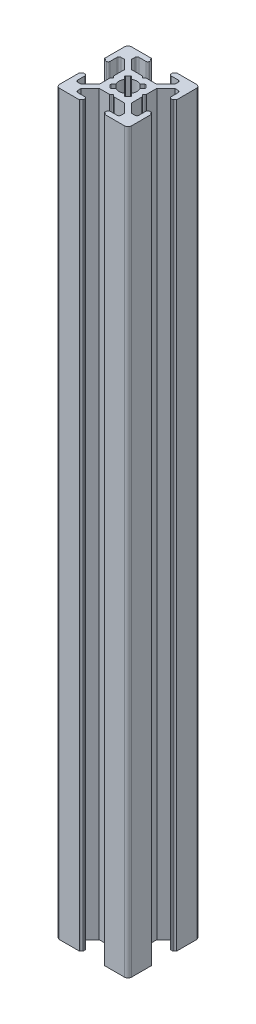
SolidWorks part; units mm, degrees
ref_plane "Front Plane" through (0, 0, 0) normal (0, 0, 1) x (1, 0, 0)
ref_plane "Top Plane" through (0, 0, 0) normal (0, 1, 0) x (1, 0, 0)
ref_plane "Right Plane" through (0, 0, 0) normal (1, 0, 0) x (0, 0, -1)
sketch "Sketch3" plane through (0, 0, 0) normal (0, 1, 0) x (1, 0, 0)
  line L0 (7, 20) -> (7, 18.5)
  line L1 (0, 0) -> (20, 0)
  line L2 (0, 0) -> (0, 20)
  line L3 (0, 20) -> (20, 20)
  line L4 (20, 0) -> (20, 20)
  line L5 (7, 18.5) -> (4, 18.5)
  line L6 (4, 18.5) -> (4, 17)
  line L7 (4, 17) -> (6.5, 14.5)
  line L8 (6.5, 14.5) -> (13.5, 14.5)
  line L9 (13.5, 14.5) -> (16, 17)
  line L10 (16, 17) -> (16, 18.5)
  line L11 (16, 18.5) -> (13, 18.5)
  line L12 (13, 18.5) -> (13, 20)
  line L13 (13, 20) -> (7, 20)
  line L14 (9.5, 14.5) -> (10, 14)
  line L15 (10, 14) -> (10.5, 14.5)
  line L16 (10.5, 14.5) -> (9.5, 14.5)
  line L17 (13, 19.5) -> (13, 20)
  line L18 (13.5, 20) -> (13, 20)
  line L19 (7, 19.5) -> (7, 20)
  line L20 (6.5, 20) -> (7, 20)
  line L21 (0, 13) -> (1.5, 13)
  line L22 (1.5, 13) -> (1.5, 16)
  line L23 (1.5, 16) -> (3, 16)
  line L24 (3, 16) -> (5.5, 13.5)
  line L25 (5.5, 13.5) -> (5.5, 6.5)
  line L26 (5.5, 6.5) -> (3, 4)
  line L27 (3, 4) -> (1.5, 4)
  line L28 (1.5, 4) -> (1.5, 7)
  line L29 (1.5, 7) -> (0, 7)
  line L30 (0, 7) -> (0, 13)
  line L31 (5.5, 10.5) -> (5.5, 9.5)
  line L32 (5.5, 9.5) -> (6, 10)
  line L33 (6, 10) -> (5.5, 10.5)
  line L34 (0.5, 13) -> (0, 13)
  line L35 (0, 13.5) -> (0, 13)
  line L36 (0, 6.5) -> (0, 7)
  line L37 (0.5, 7) -> (0, 7)
  line L38 (10, 20) -> (10, 0) construction
  line L39 (20, 10) -> (0, 10) construction
  line L40 (10, 6) -> (10.5, 5.5)
  line L41 (9.5, 5.5) -> (10, 6)
  line L42 (10.5, 5.5) -> (9.5, 5.5)
  line L43 (13.5, 0) -> (13, 0)
  line L44 (13, 0.5) -> (13, 0)
  line L45 (6.5, 0) -> (7, 0)
  line L46 (7, 0.5) -> (7, 0)
  line L47 (13, 1.5) -> (13, 0)
  line L48 (16, 1.5) -> (13, 1.5)
  line L49 (16, 3) -> (16, 1.5)
  line L50 (13.5, 5.5) -> (16, 3)
  line L51 (6.5, 5.5) -> (13.5, 5.5)
  line L52 (4, 3) -> (6.5, 5.5)
  line L53 (4, 1.5) -> (4, 3)
  line L54 (7, 1.5) -> (4, 1.5)
  line L55 (7, 0) -> (7, 1.5)
  line L56 (13, 0) -> (7, 0)
  line L57 (14.5, 9.5) -> (14, 10)
  line L58 (14.5, 10.5) -> (14.5, 9.5)
  line L59 (14, 10) -> (14.5, 10.5)
  line L60 (19.5, 7) -> (20, 7)
  line L61 (20, 6.5) -> (20, 7)
  line L62 (20, 13.5) -> (20, 13)
  line L63 (19.5, 13) -> (20, 13)
  line L64 (18.5, 7) -> (20, 7)
  line L65 (18.5, 4) -> (18.5, 7)
  line L66 (17, 4) -> (18.5, 4)
  line L67 (14.5, 6.5) -> (17, 4)
  line L68 (14.5, 13.5) -> (14.5, 6.5)
  line L69 (17, 16) -> (14.5, 13.5)
  line L70 (18.5, 16) -> (17, 16)
  line L71 (18.5, 13) -> (18.5, 16)
  line L72 (20, 13) -> (18.5, 13)
  line L73 (20, 7) -> (20, 13)
  arc A0 (13.5, 20) -> (13, 19.5) centre (13, 20) cw
  arc A1 (6.5, 20) -> (7, 19.5) centre (7, 20) ccw
  arc A2 (0.5, 13) -> (0, 13.5) centre (0, 13) ccw
  arc A3 (0.5, 7) -> (0, 6.5) centre (0, 7) cw
  arc A4 (13.5, 0) -> (13, 0.5) centre (13, 0) ccw
  arc A5 (6.5, 0) -> (7, 0.5) centre (7, 0) cw
  arc A6 (19.5, 7) -> (20, 6.5) centre (20, 7) ccw
  arc A7 (19.5, 13) -> (20, 13.5) centre (20, 13) cw
  point P7 (10, 14.5)
  point P16 (10, 20)
  point P26 (5.5, 10)
  point P35 (0, 10)
  dimension "D16" = 0.5
  dimension "D17" = 0.5
  dimension "D28" = 0.5
  dimension "D29" = 0.5
  dimension "D1" = 20
  dimension "D2" = 20
  dimension "D3" = 7
  dimension "D4" = 7
  dimension "D5" = 1.5
  dimension "D6" = 1.5
  dimension "D7" = 3
  dimension "D8" = 3
  dimension "D9" = 1.5
  dimension "D10" = 1.5
  dimension "D11" = 7
  dimension "D12" = 5.5
  dimension "D13" = 0.5
  dimension "D14" = 0.5
  dimension "D15" = 0.5
  dimension "D18" = 7
  dimension "D19" = 7
  dimension "D20" = 1.5
  dimension "D21" = 1.5
  dimension "D22" = 3
  dimension "D23" = 7
  dimension "D24" = 5.5
  dimension "D25" = 0.5
  dimension "D26" = 0.5
  dimension "D27" = 0.5
extrude "Boss-Extrude1" add sketch "Sketch3" along normal blind 205 contours L72 A7 L4 L3 A0 L12 L11 L10 L9 L8 L15 L14 L7 L6 L5 L0 A1 L2 A2 L21 L22 L23 L24 L25 L33 L32 L26 L27 L28 L29 A3 L1 A5 L55 L54 L53 L52 L51 L41 L40 L50 L49 L48 L47 A4
fillet "Fillet1" radius 1 4 edges at (0, 102.5, 0) (20, 102.5, 0) (20, 102.5, -20) (0, 102.5, -20)
sketch "Sketch4" plane through (0, 205, 0) normal (0, 1, 0) x (1, 0, 0)
  line L0 (13.5, 14.5) -> (5.5, 6.5) construction
  line L1 (14.5, 13.5) -> (6.5, 5.5) construction
  line L2 (10.5, 14.5) -> (14.5, 10.5) construction
  line L3 (12, 13) -> (13, 12)
  line L4 (13, 12) -> (8, 7)
  line L5 (8, 7) -> (7, 8)
  line L6 (7, 8) -> (12, 13)
  line L7 (13.5, 14.5) -> (16, 17) construction
  line L8 (17, 16) -> (14.5, 13.5) construction
  line L9 (5.5, 9.5) -> (9.5, 5.5) construction
  line L10 (5.5, 10.5) -> (9.5, 14.5) construction
  line L11 (14.5, 9.5) -> (10.5, 5.5) construction
  line L12 (6.5, 14.5) -> (14.5, 6.5) construction
  line L13 (5.5, 13.5) -> (13.5, 5.5) construction
  line L14 (7, 12) -> (8, 13)
  line L15 (8, 13) -> (13, 8)
  line L16 (13, 8) -> (12, 7)
  line L17 (12, 7) -> (7, 12)
  line L18 (4, 17) -> (6.5, 14.5) construction
  line L19 (3, 16) -> (5.5, 13.5) construction
  line L20 (20, 10) -> (0, 10) construction
  circle A0 centre (10, 10) radius 2.5
  dimension "D1" = 5
extrude "Cut-Extrude1" cut sketch "Sketch4" against normal through all contours L6 A0 L15 | L4 A0 L6 L15 | L15 A0 L17 L6 | L17 L4 L15 L6 | L17 A0 L6 | L6 A0 L4 L17 | L4 A0 L17 | L17 A0 L15 L4 | L15 A0 L4 | A0 L6 L5 L4 | A0 L17 L16 L15 | A0 L4 L3 L6 | A0 L15 L14 L17
fillet "Fillet2" radius 0.5 24 edges at (1.5, 102.5, -16) (1.5, 102.5, -13) (5.5, 102.5, -10.5) (5.5, 102.5, -9.5) (1.5, 102.5, -7) (1.5, 102.5, -4) (4, 102.5, -1.5) (7, 102.5, -1.5) (9.5, 102.5, -5.5) (10.5, 102.5, -5.5) (13, 102.5, -1.5) (16, 102.5, -1.5) (18.5, 102.5, -4) (18.5, 102.5, -7) (18.5, 102.5, -13) (18.5, 102.5, -16) (14.5, 102.5, -9.5) (14.5, 102.5, -10.5) (10.5, 102.5, -14.5) (9.5, 102.5, -14.5) (16, 102.5, -18.5) (13, 102.5, -18.5) (7, 102.5, -18.5) (4, 102.5, -18.5)
fillet "Fillet3" radius 0.25 8 edges at (13, 102.5, -8) (12, 102.5, -7) (13, 102.5, -12) (12, 102.5, -13) (8, 102.5, -13) (7, 102.5, -12) (7, 102.5, -8) (8, 102.5, -7)
